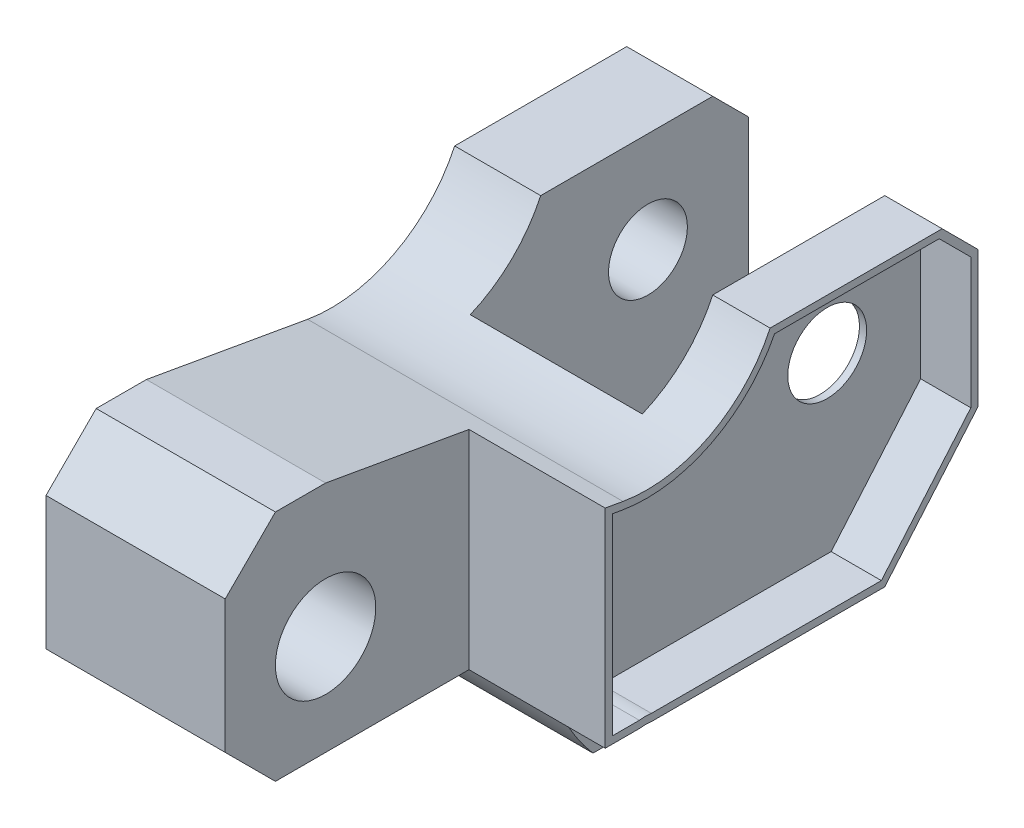
SolidWorks part; units mm, degrees
material "AISI 1020"
ref_plane "Front Plane" through (0, 0, 0) normal (0, 0, 1) x (1, 0, 0)
ref_plane "Top Plane" through (0, 0, 0) normal (0, 1, 0) x (1, 0, 0)
ref_plane "Right Plane" through (0, 0, 0) normal (1, 0, 0) x (0, 0, -1)
sketch "Sketch1" plane through (0, 0, 0) normal (1, 0, 0) x (0, 0, -1)
  line L0 (0, 0) -> (24, 0)
  line L1 (29, -5) -> (29, -24)
  line L2 (24, 0) -> (29, -5)
  line L5 (29, -24) -> (0, -58)
  line L6 (0, -58) -> (-5.703, -58)
  line L7 (-18.1588, -39.2629) -> (-50, -39.2629)
  line L8 (16.2059, -39) -> (16.0887, -38.9154)
  line L9 (16.0887, -38.9154) -> (16.2059, -39)
  line L10 (-57, -32.2629) -> (-57, -13.7176)
  line L13 (-50, -39.2629) -> (-57, -32.2629)
  line L14 (-43, -6.7176) -> (-50, -6.7176)
  line L15 (-57, -13.7176) -> (-50, -6.7176)
  line L16 (-43, -6.7176) -> (-20.5192, -10.6816)
  line L19 (-23, -24) -> (-23, -23.8851)
  line L21 (16.0887, -38.9154) -> (-18.1588, -39.2629)
  arc A0 (-9.519, -52.3876) -> (-5.703, -58) centre (16.2059, -39) ccw
  arc A1 (-9.519, -52.3876) -> (-12.4524, -43.4387) centre (16.2059, -39) cw
  arc A2 (-12.4524, -43.4387) -> (-18.1588, -39.2629) centre (-17.3935, -44.204) ccw
  circle A3 centre (-43, -25.2629) radius 7
  arc A4 (-20.5192, -10.6816) -> (0, 0) centre (-17.2198, 8.0297) ccw
  point P1 (29, 0)
  point P6 (-7.7758, -55.3058)
  point P7 (-57, -39.2629)
  point P19 (-57, -6.7176)
  dimension "D7" = 86
  dimension "D11" = 14
  dimension "D18" = 19
  dimension "D19" = 5
  dimension "D20" = 14
  dimension "D1" = 29
  dimension "D2" = 24
  dimension "D3" = 5
  dimension "D4" = 45
  dimension "D5" = 19
  dimension "D6" = 29
  dimension "D8" = 58
  dimension "D9" = 7
  dimension "D10" = 45
  dimension "D12" = 7
  dimension "D13" = 45
  dimension "D14" = 14
  dimension "D15" = 14
  dimension "D16" = 29
  dimension "D17" = 10
extrude "Boss-Extrude3" add sketch "Sketch1" along normal mid plane 44 contours A3 | A4 L0 L2 L1 L5 L6 A0 A1 A2 L7 L13 L10 L15 L14 L16
sketch "Sketch8" plane through (22, 0, 0) normal (1, 0, 0) x (0, 0, -1)
  circle A0 centre (14.9629, -14) radius 5.5
  dimension "D1" = 11
extrude "Cut-Extrude1" cut sketch "Sketch8" against normal blind 46
sketch "Sketch10" plane through (22, 0, 0) normal (1, 0, 0) x (0, 0, -1)
  line L1 (-18.1588, -39.2629) -> (-50, -39.2629) construction
  line L2 (-57.0591, -6.6658) -> (-23, -6.6658)
  line L3 (-57.0591, -6.6658) -> (-57.0591, -39.2629)
  line L4 (-57.0591, -39.2629) -> (-23, -39.2629)
  line L5 (-23, -6.6658) -> (-23, -39.2629)
  dimension "D1" = 52
extrude "Cut-Extrude2" cut sketch "Sketch10" against normal blind 19 contours L3 L2 L5 L4
sketch "Sketch19" plane through (0, 0, 0) normal (1, 0, 0) x (0, 0, -1)
  line L0 (29, -5) -> (29, 6.7501)
  line L3 (29, -24) -> (0, -58) construction
  arc A1 (18.7647, -36) -> (-9.8257, -9.4725) centre (29, 3.7019) cw
  arc A2 (-20.5192, -10.6816) -> (0, 0) centre (-17.2198, 8.0297) ccw construction
  circle A3 centre (29, 3.7019) radius 41
  dimension "D1" = 41
extrude "Cut-Extrude5" cut sketch "Sketch19" against normal blind 10 and the other way blind 14 contours A3
sketch "Sketch21" plane through (22, 0, 0) normal (1, 0, 0) x (0, 0, -1)
  line L1 (-23, -39.2629) -> (16.0401, -39.2629)
  line L2 (-23, -39.2629) -> (-23, -58.2629)
  line L3 (-23, -58.2629) -> (16.0401, -58.2629)
  line L4 (16.0401, -39.2629) -> (16.0401, -58.2629)
extrude "Cut-Extrude7" cut sketch "Sketch21" against normal blind 19
sketch "Sketch22" plane through (22, 0, 0) normal (1, 0, 0) x (0, 0, -1)
  line L16 (-16.5548, -38.2629) -> (15.5202, -38.2629)
  line L17 (15.5202, -38.2629) -> (28, -23.6315)
  line L18 (28, -23.6315) -> (28, -5.4142)
  line L19 (28, -5.4142) -> (23.5858, -1)
  line L20 (23.5858, -1) -> (0.6257, -1)
  line L21 (-20.6928, -11.6664) -> (-22, -11.4359)
  line L22 (-22, -11.4359) -> (-22, -38.2629)
  line L23 (-22, -38.2629) -> (-18.2322, -38.2629)
  line L24 (-16.5548, -38.2629) -> (15.5202, -38.2629)
  line L25 (15.5202, -38.2629) -> (28, -23.6315)
  line L26 (28, -23.6315) -> (28, -5.4142)
  line L27 (28, -5.4142) -> (23.5858, -1)
  line L28 (23.5858, -1) -> (0.6257, -1)
  line L29 (-20.6928, -11.6664) -> (-22, -11.4359)
  line L30 (-22, -11.4359) -> (-22, -38.2629)
  line L31 (-22, -38.2629) -> (-18.2322, -38.2629)
  arc A4 (-20.6928, -11.6664) -> (0.6257, -1) centre (-17.2198, 8.0297) ccw
  arc A5 (-16.5548, -38.2629) -> (-18.2322, -38.2629) centre (-17.3935, -44.204) ccw
  arc A6 (-20.6928, -11.6664) -> (0.6257, -1) centre (-17.2198, 8.0297) ccw
  arc A7 (-16.5548, -38.2629) -> (-18.2322, -38.2629) centre (-17.3935, -44.204) ccw
  dimension "D1" = 1
extrude "Cut-Extrude8" cut sketch "Sketch22" against normal blind 7
